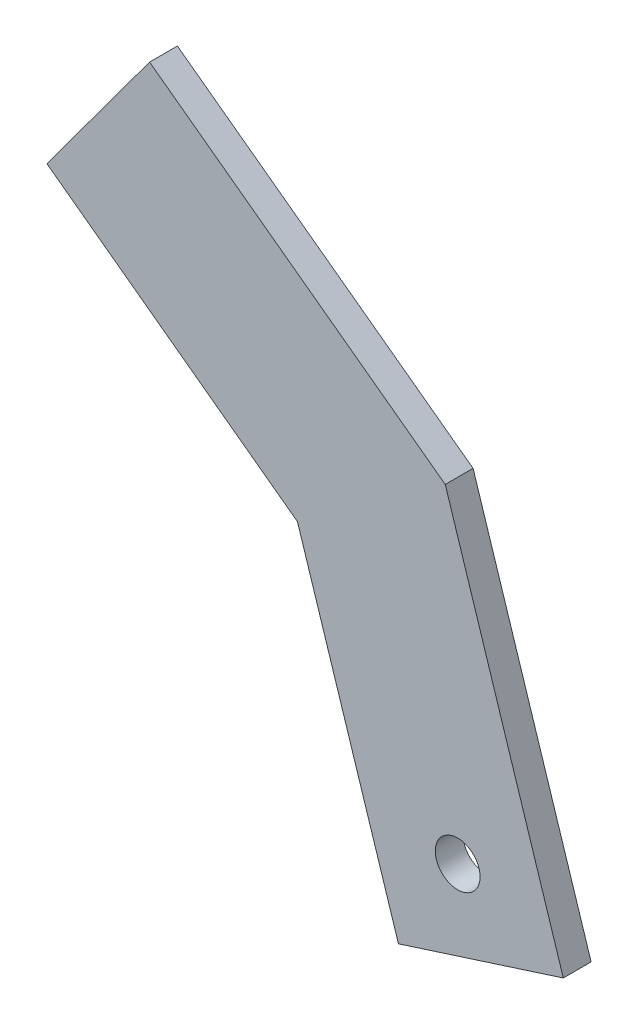
SolidWorks part; units mm, degrees
ref_plane "Front Plane" through (0, 0, 0) normal (0, 0, 1) x (1, 0, 0)
ref_plane "Top Plane" through (0, 0, 0) normal (0, 1, 0) x (1, 0, 0)
ref_plane "Right Plane" through (0, 0, 0) normal (1, 0, 0) x (0, 0, -1)
sketch "Sketch1" plane through (0, 0, 0) normal (0, 0, 1) x (1, 0, 0)
  line L0 (-8.9266, 231.7201) -> (75.9128, -33.0537)
  line L1 (75.9128, -33.0537) -> (-42.5662, -71.017)
  line L2 (-42.5662, -71.017) -> (-115.1283, 155.4409)
  line L3 (0, 0) -> (16.6733, -52.0353) construction
  line L4 (-8.9266, 231.7201) -> (-221.4098, 388.3256)
  line L5 (-221.4098, 388.3256) -> (-295.2231, 288.1754)
  line L6 (-295.2231, 288.1754) -> (-115.1283, 155.4409)
  circle A0 centre (0, 0) radius 101.6 construction
  circle A1 centre (0, 0) radius 16.1026
  dimension "D1" = 203.2
extrude "Boss-Extrude1" add sketch "Sketch1" along normal blind 20 contours L4 L5 L6 L2 L1 L0 | A1
